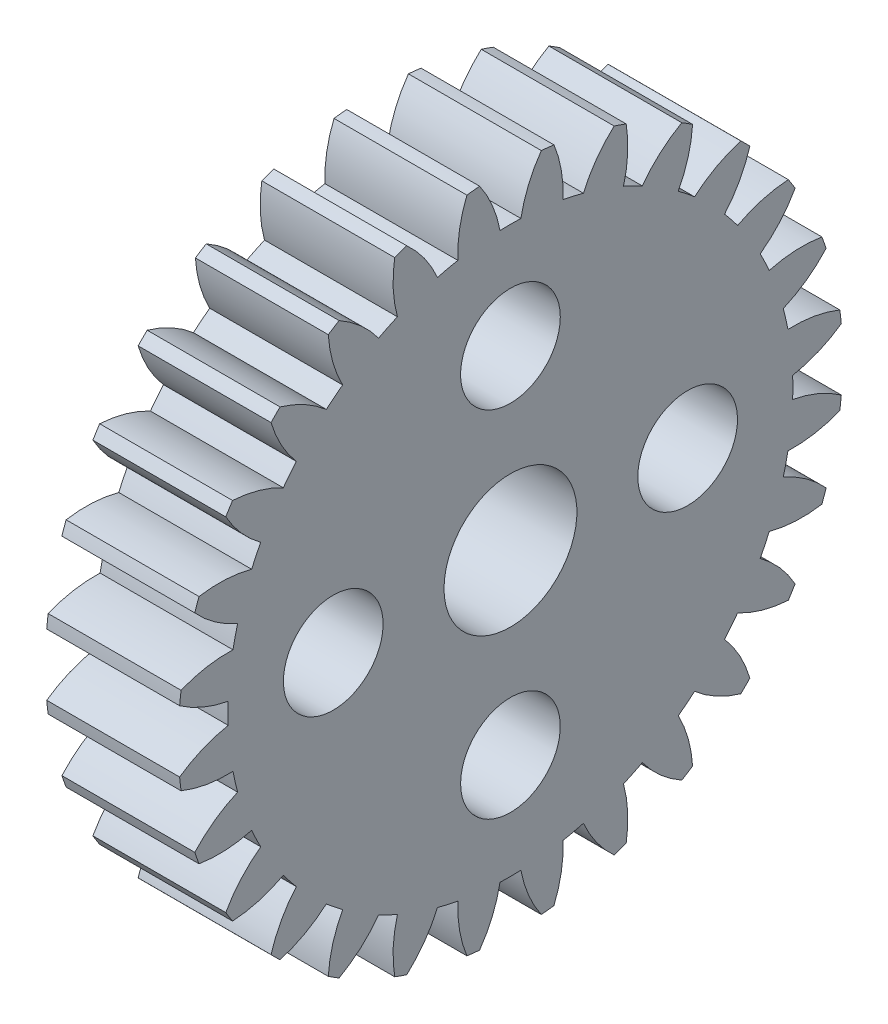
SolidWorks part; units mm, degrees
ref_plane "Plane1" through (0, 0, 0) normal (0, 0, 1) x (1, 0, 0)
ref_plane "Plane2" through (0, 0, 0) normal (0, 1, 0) x (1, 0, 0)
ref_plane "Plane3" through (0, 0, 0) normal (1, 0, 0) x (0, 0, -1)
sketch "HoldingSke" plane through (0, 0, 0) normal (0, 1, 0) x (1, 0, 0)
  line L0 (0, 0) -> (0.8829, -0.4695)
  line L1 (-15, 0) -> (100, 0) construction
  line L2 (0, 0) -> (-2.1039, 2.3779)
  line L3 (0, 0) -> (-11.863, 4.5341)
  line L4 (0, 0) -> (7.6251, 4.0544)
  line L5 (0, 0) -> (-46.8476, -17.4728)
  line L6 (0, 0) -> (-3.3159, -2.2372)
  line L7 (-2.1039, 2.3779) -> (8.6586, 51.2059)
  line L8 (-76.2, 54.61) -> (-75.2, 54.61)
  line L9 (-71.009, 38.7566) -> (-53.1078, 45.2721)
  line L10 (-76.2, 71.12) -> (104.1128, 71.12)
  line L11 (0, 0) -> (-4, 0)
  line L12 (-76.2, 101.6) -> (-76.162, 101.6)
  line L13 (24.9733, 27.94) -> (52.9518, 28.4284)
  line L14 (24.9733, 27.94) -> (24.9743, 27.94)
  line L15 (24.9733, 27.94) -> (100.4006, 29.5858)
  line L16 (-63.627, -1) -> (-12.827, -1)
  circle A0 centre (0, 0) radius 3
  circle A1 centre (0, 0) radius 12.749
  circle A2 centre (0, 0) radius 37.5
  circle A3 centre (0, 0) radius 3
  dimension "MHD" = 25.498
  dimension "Hub_dia" = 75
  dimension "Bore" = 6
  dimension "MBD" = 6
  dimension "Num_teeth" = 28
  dimension "Pitch" = 1
  dimension "Overall_len" = 50
  dimension "Show_teeth" = 28
  dimension "Thickness" = 4
  dimension "OAL" = 50.0001
  dimension "T_dim" = 1
  dimension "Ap" = 20
  dimension "H" = 19.05
  dimension "Pitch_radius" = 180.3128
  dimension "Width" = 4
  dimension "Backlash" = 0.038
  dimension "Addendum_fac" = 1
  dimension "Dedendum_fac" = 1.25
  dimension "Clearance_fac" = 0.25
  dimension "Dedendum_add" = 0.001
  dimension "Module" = 1
sketch "BasProSke" plane through (0, 0, 0) normal (0, 1, 0) x (1, 0, 0)
  line L0 (-10, 0) -> (60, 0) construction
  line L1 (0, 0) -> (0, 15)
  line L2 (0, 0) -> (6, 0)
  line L3 (6, 0) -> (6, 15)
  line L4 (6, 15) -> (0, 15)
  dimension "Thickness" = 6
  dimension "Diameter" = 30
revolve "Base-Revolve" add sketch "BasProSke" angle 360 about L0
sketch "TooCutSke" plane through (0, 0, 0) normal (1, 0, 0) x (0, 0, -1)
  line L1 (0, 0) -> (0, 107) construction
  line L2 (0, 0) -> (-0.8515, 13.9741) construction
  line L3 (0, 0) -> (-3.1309, 27.7873) construction
  line L4 (-0.8515, 13.9741) -> (-1.5654, 13.8936) construction
  arc A0 (0.4713, 12.7403) -> (-0.4713, 12.7403) centre (0, 0) ccw
  arc A1 (1.4098, 14.9591) -> (-1.4098, 14.9591) centre (0, 0) ccw
  circle A2 centre (0, 0) radius 14 construction
  circle A3 centre (0, 0) radius 13.1557 construction
  arc A4 (-0.4713, 12.7403) -> (-1.4098, 14.9591) centre (-5.9775, 11.7193) ccw
  arc A5 (1.4098, 14.9591) -> (0.4713, 12.7403) centre (5.9775, 11.7193) ccw
  dimension "Root_dia" = 25.498
  dimension "Overcut_dia" = 30.0508
  dimension "Pitch_dia" = 28
  dimension "Base_dia" = 26.3114
  dimension "Flank_rad" = 5.6
  dimension "Half_ang" = 6.429
  dimension "Half_CT" = 0.7185
extrude "ToothCut" cut sketch "TooCutSke" along normal through all
fillet "Breaks" [suppressed] radius 0.02
fillet "RootFillets" [suppressed] radius 0.251
pattern_circular "TeethCuts" count 28 every 12.857 about axis through (-10, 0, 0) along (1, 0, 0) of "ToothCut", "RootFillets", "Breaks"
sketch "HubNeaOneSke" plane through (0, 0, 0) normal (-1, 0, 0) x (0, 0, 1)
  circle A0 centre (0, 0) radius 12.749
  dimension "Diameter" = 25.498
extrude "HubNearOne" [suppressed] add sketch "HubNeaOneSke" along normal blind 44.0001
sketch "HubNeaBotSke" plane through (0, 0, 0) normal (-1, 0, 0) x (0, 0, 1)
  circle A0 centre (0, 0) radius 12.749
  dimension "Diameter" = 25.498
extrude "HubNearBoth" [suppressed] add sketch "HubNeaBotSke" along normal blind 22
ref_plane "FarPln" through (6, 0, 0) normal (1, 0, 0) x (0, 0, -1)
sketch "HubFarSke" plane through (6, 0, 0) normal (1, 0, 0) x (0, 0, -1)
  circle A0 centre (0, 0) radius 12.749
  dimension "Diameter" = 25.498
extrude "HubFar" [suppressed] add sketch "HubFarSke" along normal blind 22
sketch "BorSke" plane through (0, 0, 0) normal (1, 0, 0) x (0, 0, -1)
  circle A0 centre (0, 0) radius 3
  dimension "Diameter" = 6
extrude "Bore" cut sketch "BorSke" along normal mid plane 100.0001
sketch "KeySke" plane through (0, 0, 0) normal (1, 0, 0) x (0, 0, -1)
  line L0 (-1, 0) -> (-1, 4)
  line L1 (-1, 4) -> (1, 4)
  line L2 (1, 4) -> (1, 0)
  line L3 (0, 0) -> (0, 34) construction
  line L4 (-1, 0) -> (1, 0)
  dimension "Offset" = 4
  dimension "Width" = 2
extrude "Keyway" [suppressed] cut sketch "KeySke" along normal mid plane 100.0001
pattern_circular "Keyway2" [suppressed] count 2 every 90 about axis through (-10, 0, 0) along (1, 0, 0)
hole_wizard "M4 Clearance Hole1" positions "Sketch1" profile "Sketch2" hole size "M4" standard "ANSI Metric" end condition through all
sketch "Sketch1" plane through (6, 0, 0) normal (1, 0, 0) x (0, 0, -1)
  line L0 (0, 0) -> (0, 8) construction
  point P2 (0, 8)
  dimension "D1" = 8
sketch "Sketch2" plane through (6, 8, 0) normal (0, 1, 0) x (0, 0, -1)
  line L0 (0, 0) -> (0, 6)
  line L1 (0, 6) -> (2.25, 6)
  line L2 (2.25, 6) -> (2.25, 0)
  line L5 (2.25, 0) -> (0, 0)
  line L11 (0, -6.35) -> (0, 107.95) construction
  dimension "Thru Hole Dia." = 4.5
  dimension "Thru Hole Depth" = 6
pattern_circular "CirPattern1" count 4 over 360 about axis through (0, 0, 0) along (1, 0, 0) of "M4 Clearance Hole1"
equation "' \"Module@HoldingSke\" = 6.35"
equation "' \"Num_teeth@HoldingSke\" = 12"
equation "' \"Ap@HoldingSke\" =  20"
equation "' \"Ap@HoldingSke\" = 20"
equation "' \"Width@HoldingSke\" = 0.5 * 25.4"
equation "' \"Hub_dia@HoldingSke\"= 1 * 25.4"
equation "' \"Hub_dia@HoldingSke\" = 1 * 25.4"
equation "' \"Overall_len@HoldingSke\" = 1.0 * 25.4"
equation "' \"Bore@HoldingSke\" = 0.75 * 25.4"
equation "' \"T_dim@HoldingSke\" = 0.1 * 25.4"
equation "' \"Width@KeySke\" = 0.25 * 25.4"
equation "' \"Show_teeth@HoldingSke\" = 13"
equation "' \"Backlash@HoldingSke\" = 0.009 * 25.4"
equation "' \"Addendum_fac@HoldingSke\" = 1.0"
equation "' \"Dedendum_fac@HoldingSke\" = 1.25"
equation "' \"Dedendum_add@HoldingSke\" = 0.00005 * 25.4"
equation "' \"Clearance_fac@HoldingSke\" = 0.25"
equation "\"Pitch@HoldingSke\" = 1 / \"Module@HoldingSke\""
equation "\"Overcut_dia@TooCutSke\" = (\"Num_teeth@HoldingSke\" + 2 * \"Addendum_fac@HoldingSke\") / \"Pitch@HoldingSke\" + 0.002 * 25.4"
equation "\"Pitch_dia@TooCutSke\" = \"Num_teeth@HoldingSke\" / \"Pitch@HoldingSke\""
equation "\"Base_dia@TooCutSke\" = \"Num_teeth@HoldingSke\" / \"Pitch@HoldingSke\" * cos((\"Ap@HoldingSke\"  * 3.14159265 / 180))"
equation "\"Root_dia@TooCutSke\" = (\"Num_teeth@HoldingSke\" + 2) / \"Pitch@HoldingSke\" - 2 * (\"Addendum_fac@HoldingSke\" + \"Dedendum_fac@HoldingSke\") / \"Pitch@HoldingSke\" - \"Dedendum_add@HoldingSke\" * 2"
equation "\"Half_ang@TooCutSke\" = 180 / \"Num_teeth@HoldingSke\""
equation "\"Half_CT@TooCutSke\" = \"Num_teeth@HoldingSke\" / \"Pitch@HoldingSke\" * sin((3.14159265 / 2 / \"Num_teeth@HoldingSke\")) / 2 - 7 * \"Backlash@HoldingSke\" / 4"
equation "\"Flank_rad@TooCutSke\" = \"Num_teeth@HoldingSke\" / \"Pitch@HoldingSke\" / 5"
equation "\"Radius@RootFillets\" = \"Clearance_fac@HoldingSke\" / \"Pitch@HoldingSke\" + \"Dedendum_add@HoldingSke\""
equation "\"Break_rad@Breaks\" = 0.02 / \"Pitch@HoldingSke\""
equation "\"Thickness@HoldingSke\" = \"Width@HoldingSke\""
equation "\"OAL@HoldingSke\" = \"Thickness@HoldingSke\""
equation "\"MHD@HoldingSke\" = (\"Num_teeth@HoldingSke\" + 2) / \"Pitch@HoldingSke\" - 2 * (\"Addendum_fac@HoldingSke\" + \"Dedendum_fac@HoldingSke\")  / \"Pitch@HoldingSke\" - \"Dedendum_add@HoldingSke\" * 2"
equation "\"MBD@HoldingSke\" = (\"Num_teeth@HoldingSke\" + 2) / \"Pitch@HoldingSke\" - 2 * (\"Addendum_fac@HoldingSke\" + \"Dedendum_fac@HoldingSke\")  / \"Pitch@HoldingSke\" - \"Dedendum_add@HoldingSke\" * 2 - 0.002 * 25.4"
equation "\"MHD@HoldingSke\" = ((sgn( \"MHD@HoldingSke\" - \"Hub_dia@HoldingSke\" )-1)*( \"MHD@HoldingSke\" - \"Hub_dia@HoldingSke\" ))/-2+ \"Hub_dia@HoldingSke\""
equation "\"MBD@HoldingSke\" = ((sgn( \"MBD@HoldingSke\" - \"Bore@HoldingSke\" )-1)*( \"MBD@HoldingSke\" - \"Bore@HoldingSke\" ))/-2+ \"Bore@HoldingSke\""
equation "\"OAL@HoldingSke\" = ((sgn( \"OAL@HoldingSke\" - \"Overall_len@HoldingSke\" )+1)*( \"OAL@HoldingSke\" - \"Overall_len@HoldingSke\" ))/2 + \"Overall_len@HoldingSke\" + 0.000002 * 25.4"
equation "\"Num_teeth@TeethCuts\" = int( \"Show_teeth@HoldingSke\" ) + 1"
equation "\"Num_teeth@TeethCuts\" = ((sgn( \"Num_teeth@TeethCuts\" - \"Num_teeth@HoldingSke\" )-1)*( \"Num_teeth@TeethCuts\" - \"Num_teeth@HoldingSke\" ))/-2+ \"Num_teeth@HoldingSke\""
equation "\"Num_teeth@TeethCuts\" = ((sgn( \"Num_teeth@TeethCuts\" - 2.0)+1)*( \"Num_teeth@TeethCuts\" - 2.0))/2 +2.0"
equation "\"Angle@TeethCuts\" = 360.0 / \"Num_teeth@HoldingSke\""
equation "\"Diameter@BasProSke\" = (\"Num_teeth@HoldingSke\" + 2 * \"Addendum_fac@HoldingSke\") / \"Pitch@HoldingSke\""
equation "' \"Fillet_rad@BasProSke\" =  \"Thickness@HoldingSke\" * 0.05"
equation "' \"Fillet_rad@BasProSke\" = \"Thickness@HoldingSke\" * 0.05"
equation "\"MHD@HoldingSke\" = ((sgn( \"MHD@HoldingSke\" - \"Root_dia@TooCutSke\" )-1)*( \"MHD@HoldingSke\" - \"Root_dia@TooCutSke\" ))/-2+ \"Root_dia@TooCutSke\""
equation "\"Diameter@HubNeaOneSke\" = \"MHD@HoldingSke\""
equation "\"Length@HubNearOne\" = \"OAL@HoldingSke\" - \"Thickness@BasProSke\""
equation "\"Diameter@HubNeaBotSke\" = \"MHD@HoldingSke\""
equation "\"Length@HubNearBoth\" = ( \"OAL@HoldingSke\" - \"Thickness@BasProSke\" ) / 2.0"
equation "\"Thickness@FarPln\" = \"Thickness@BasProSke\""
equation "\"Diameter@HubFarSke\" = \"MHD@HoldingSke\""
equation "\"Length@HubFar\" = ( \"OAL@HoldingSke\" - \"Thickness@BasProSke\" ) / 2.0"
equation "\"Diameter@BorSke\" = \"MBD@HoldingSke\""
equation "\"D1@Bore\" = \"OAL@HoldingSke\" * 2.0"
equation "\"D1@Keyway\" = \"OAL@HoldingSke\" * 2.0"
equation "\"Offset@KeySke\" = \"T_dim@HoldingSke\" + \"MBD@HoldingSke\" / 2.0"
